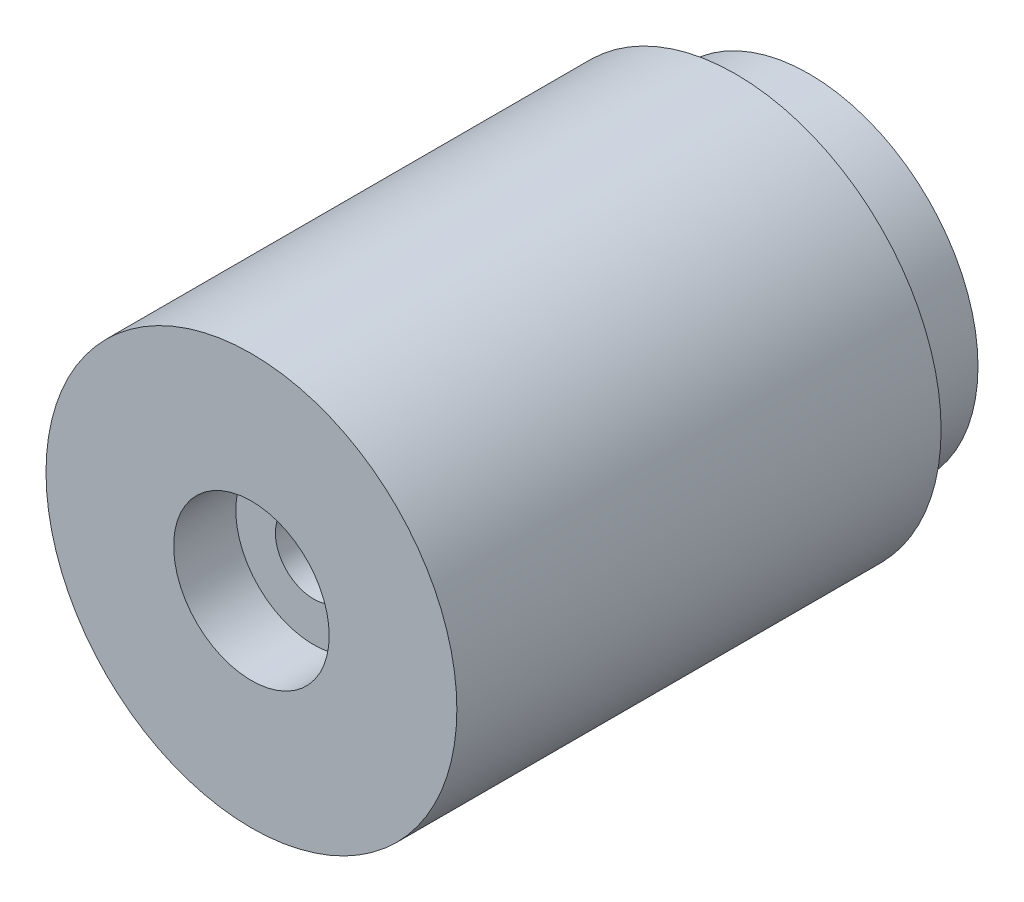
SolidWorks part; units mm, degrees
material "CA"
ref_plane "Alzado" through (0, 0, 0) normal (0, 0, 1) x (1, 0, 0)
ref_plane "Planta" through (0, 0, 0) normal (0, 1, 0) x (1, 0, 0)
ref_plane "Vista lateral" through (0, 0, 0) normal (1, 0, 0) x (0, 0, -1)
sketch "Croquis1" plane through (0, 0, 0) normal (0, 0, 1) x (1, 0, 0)
  circle A0 centre (0, 0) radius 21
  dimension "D2" = 42
extrude "Saliente-Extruir1" add sketch "Croquis1" along normal blind 49.5 contours A0
sketch "Croquis3" plane through (0, 0, 0) normal (0, 0, -1) x (-1, 0, 0)
  circle A0 centre (0, 0) radius 3.9
  dimension "D1" = 7.8
extrude "Cortar-Extruir1" cut sketch "Croquis3" against normal through all contours A0
sketch "Croquis4" plane through (0, 0, 0) normal (0, 0, -1) x (-1, 0, 0)
  circle A0 centre (0, 0) radius 17.272
  dimension "D1" = 34.544
extrude "Saliente-Extruir2" add sketch "Croquis4" along normal blind 7.5 contours A0
sketch "Croquis5" plane through (0, 0, -7.5) normal (0, 0, -1) x (-1, 0, 0)
  circle A0 centre (0, 0) radius 3.9
  dimension "D1" = 7.8
extrude "Cortar-Extruir2" cut sketch "Croquis5" against normal blind 7.5
sketch "Croquis6" plane through (0, 0, -7.5) normal (0, 0, -1) x (-1, 0, 0)
  circle A0 centre (0, 0) radius 7.95
  dimension "D1" = 15.9
extrude "Cortar-Extruir3" cut sketch "Croquis6" against normal blind 6.35
sketch "Croquis7" plane through (0, 0, 49.5) normal (0, 0, 1) x (1, 0, 0)
  circle A0 centre (0, 0) radius 7.95
  dimension "D1" = 15.9
extrude "Cortar-Extruir4" cut sketch "Croquis7" against normal blind 6.35 contours A0
